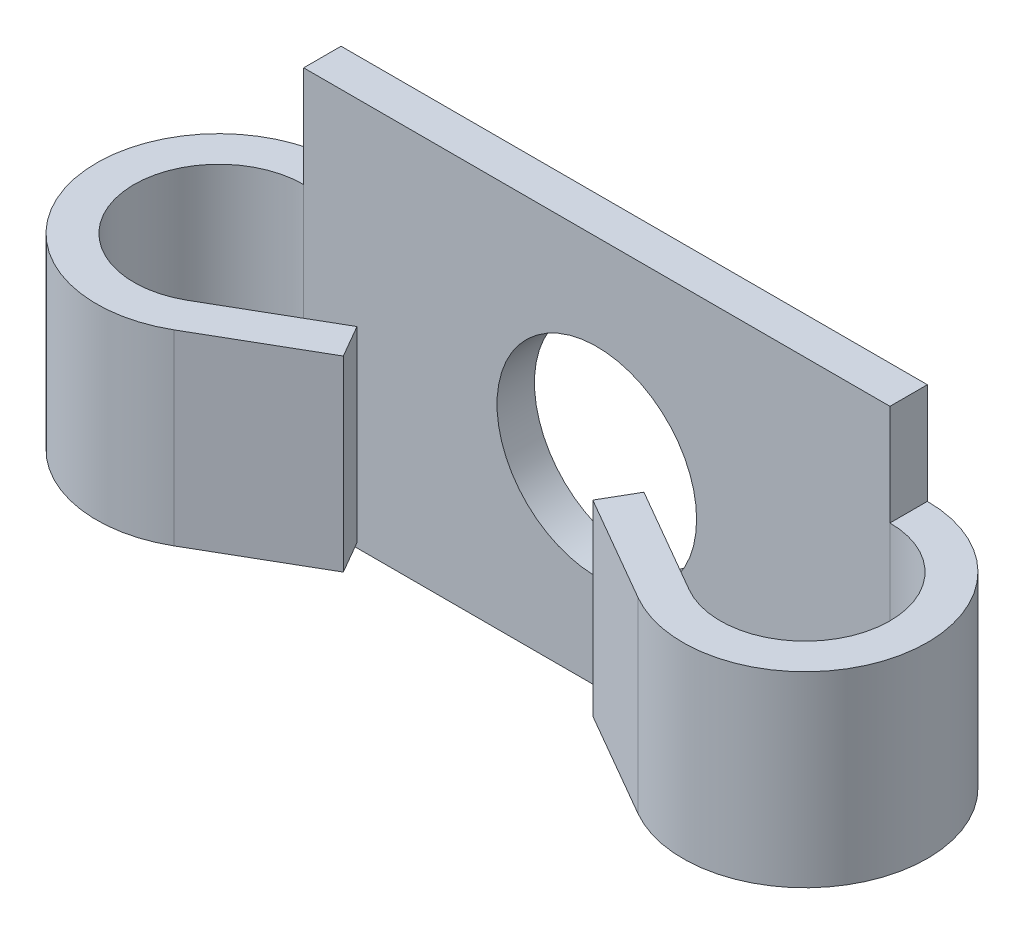
SolidWorks part; units mm, degrees
ref_plane "Спереди" through (0, 0, 0) normal (0, 0, 1) x (1, 0, 0)
ref_plane "Сверху" through (0, 0, 0) normal (0, 1, 0) x (1, 0, 0)
ref_plane "Справа" through (0, 0, 0) normal (1, 0, 0) x (0, 0, -1)
sketch "Эскиз1" plane through (0, 0, 0) normal (0, 0, 1) x (1, 0, 0)
  line L1 (-11.75, -7.8) -> (11.75, -7.8)
  line L2 (-11.75, -7.8) -> (-11.75, 7.8)
  line L3 (-11.75, 7.8) -> (11.75, 7.8)
  line L4 (11.75, -7.8) -> (11.75, 7.8)
  line L5 (-11.75, -7.8) -> (11.75, 7.8) construction
  line L6 (-11.75, 7.8) -> (11.75, -7.8) construction
  circle A0 centre (0, 0) radius 4
  point P0 (0, 0)
  dimension "D3" = 8
  dimension "D1" = 23.5
  dimension "D2" = 15.6
extrude "Бобышка-Вытянуть1" add sketch "Эскиз1" along normal blind 1.5
sketch "Эскиз3" plane through (0, 0, 0) normal (0, 1, 0) x (1, 0, 0)
  line L0 (11.75, -1.5) -> (-11.75, -1.5) construction
  line L1 (11.75, 0) -> (-11.75, 0) construction
  line L2 (-10.05, -7.8445) -> (-5.75, -5.3619)
  line L3 (-5.75, -5.3619) -> (-5, -6.6609)
  line L4 (-5, -6.6609) -> (-9.3, -9.1435)
  line L5 (-11.75, -8.3) -> (-11.75, 0) construction
  line L6 (-4, 0) -> (-4, -1.5) construction
  line L7 (-11.75, -1.5) -> (-11.75, 0)
  arc A0 (-11.75, -1.5) -> (-10.05, -7.8445) centre (-11.75, -4.9) ccw
  arc A1 (-11.75, 0) -> (-9.3, -9.1435) centre (-11.75, -4.9) ccw
  dimension "D1" = 8.3
  dimension "D2" = 30
  dimension "D3" = 1
extrude "Бобышка-Вытянуть2" add sketch "Эскиз3" along normal mid plane 7.5
mirror "Зеркальное отражение1" about plane through (0, 0, 0) normal (1, 0, 0) of "Бобышка-Вытянуть2"
